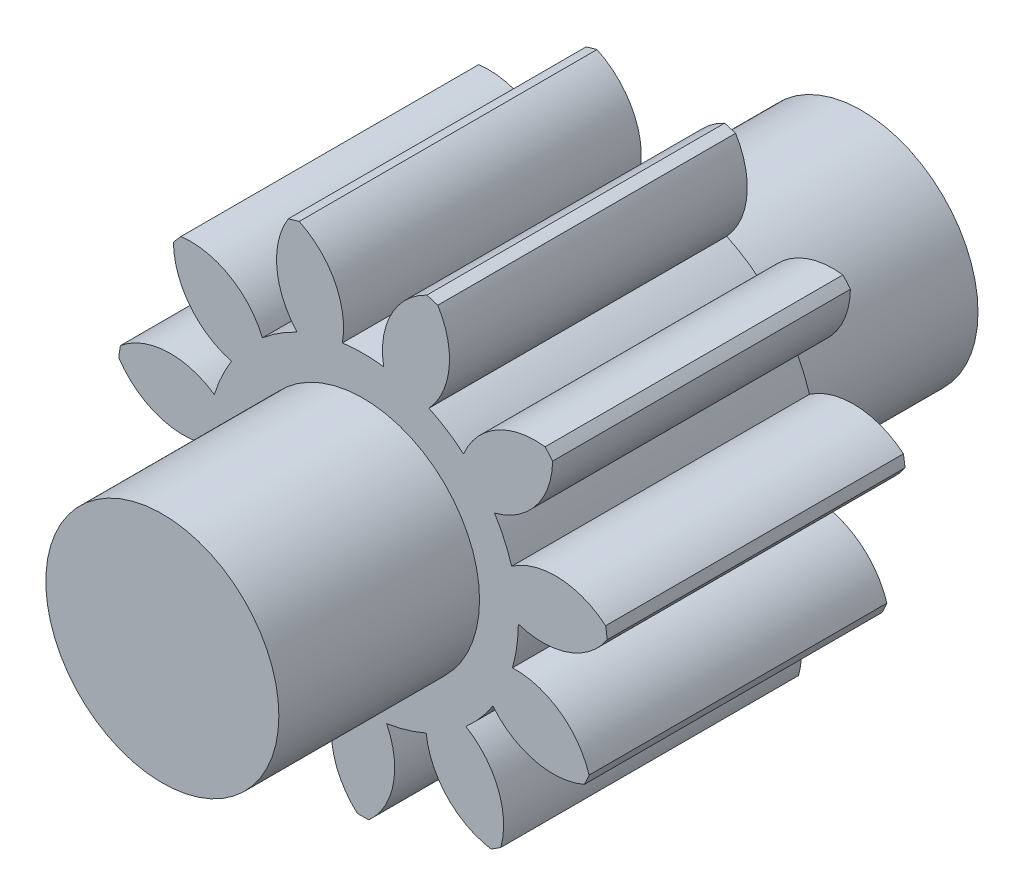
SolidWorks part; units mm, degrees
ref_plane "Front Plane" through (0, 0, 0) normal (0, 0, 1) x (1, 0, 0)
ref_plane "Top Plane" through (0, 0, 0) normal (0, 1, 0) x (1, 0, 0)
ref_plane "Right Plane" through (0, 0, 0) normal (1, 0, 0) x (0, 0, -1)
sketch "Sketch1" plane through (0, 0, 0) normal (0, 0, 1) x (1, 0, 0)
  circle A0 centre (0, 0) radius 9
  dimension "D1" = 18
extrude "Boss-Extrude1" add sketch "Sketch1" along normal mid plane 54
sketch "Sketch2" plane through (0, 0, 0) normal (0, 0, 1) x (1, 0, 0)
  line L0 (0, 35.33) -> (0, -35.33) construction
  arc A1 (1.5924, 11.8939) -> (-1.5924, 11.8939) centre (0, 0) ccw
  arc A3 (1.823, -11.8607) -> (0.443, -18.9948) centre (-3.555, -14.5209) cw
  arc A4 (-1.823, -11.8607) -> (-0.443, -18.9948) centre (3.555, -14.5209) ccw
  arc A5 (-14.0652, 12.7738) -> (-14.6454, 12.1042) centre (0, 0) ccw
  arc A8 (-4.8788, -10.9635) -> (-9.8967, -16.219) centre (-10.8413, -10.2938) cw
  arc A9 (-7.946, -8.9923) -> (-10.6421, -15.74) centre (-4.8599, -14.1378) ccw
  arc A10 (-10.0316, -6.5854) -> (-17.0943, -8.2937) centre (-14.6855, -2.7984) cw
  arc A11 (-11.5462, -3.2689) -> (-17.4623, -7.4878) centre (-11.7319, -9.266) ccw
  arc A12 (-11.9994, -0.1165) -> (-18.8645, 2.2648) centre (-13.8672, 5.5854) cw
  arc A13 (-11.4806, 3.4924) -> (-18.7385, 3.1417) centre (-14.8791, -1.4523) ccw
  arc A14 (-10.1575, 6.3894) -> (-14.6454, 12.1042) centre (-8.6461, 12.1959) cw
  arc A15 (-7.7699, 9.1448) -> (-14.0652, 12.7738) centre (-13.3023, 6.8225) ccw
  arc A16 (-5.0907, 10.8667) -> (-5.7765, 18.1006) centre (-0.68, 14.9343) cw
  arc A17 (-1.5924, 11.8939) -> (-4.9264, 18.3502) centre (-7.5021, 12.9312) ccw
  arc A18 (1.5924, 11.8939) -> (4.9264, 18.3502) centre (7.5021, 12.9312) cw
  arc A19 (5.0907, 10.8667) -> (5.7765, 18.1006) centre (0.68, 14.9343) ccw
  arc A20 (7.7699, 9.1448) -> (14.0652, 12.7738) centre (13.3023, 6.8225) cw
  arc A21 (10.1575, 6.3894) -> (14.6454, 12.1042) centre (8.6461, 12.1959) ccw
  arc A22 (11.4806, 3.4924) -> (18.7385, 3.1417) centre (14.8791, -1.4523) cw
  arc A23 (11.9994, -0.1165) -> (18.8645, 2.2648) centre (13.8672, 5.5854) ccw
  arc A24 (11.5462, -3.2689) -> (17.4623, -7.4878) centre (11.7319, -9.266) cw
  arc A25 (10.0316, -6.5854) -> (17.0943, -8.2937) centre (14.6855, -2.7984) ccw
  arc A26 (7.946, -8.9923) -> (10.6421, -15.74) centre (4.8599, -14.1378) cw
  arc A27 (4.8788, -10.9635) -> (9.8967, -16.219) centre (10.8413, -10.2938) ccw
  arc A28 (-18.7385, 3.1417) -> (-18.8645, 2.2648) centre (0, 0) ccw
  arc A29 (-4.9264, 18.3502) -> (-5.7765, 18.1006) centre (0, 0) ccw
  arc A30 (5.7765, 18.1006) -> (4.9264, 18.3502) centre (0, 0) ccw
  arc A31 (14.6454, 12.1042) -> (14.0652, 12.7738) centre (0, 0) ccw
  arc A32 (18.8645, 2.2648) -> (18.7385, 3.1417) centre (0, 0) ccw
  arc A33 (17.0943, -8.2937) -> (17.4623, -7.4878) centre (0, 0) ccw
  arc A34 (9.8967, -16.219) -> (10.6421, -15.74) centre (0, 0) ccw
  arc A35 (-0.443, -18.9948) -> (0.443, -18.9948) centre (0, 0) ccw
  arc A36 (-10.6421, -15.74) -> (-9.8967, -16.219) centre (0, 0) ccw
  arc A37 (-17.4623, -7.4878) -> (-17.0943, -8.2937) centre (0, 0) ccw
  arc A38 (7.7699, 9.1448) -> (5.0907, 10.8667) centre (0, 0) ccw
  arc A39 (11.4806, 3.4924) -> (10.1575, 6.3894) centre (0, 0) ccw
  arc A40 (11.5462, -3.2689) -> (11.9994, -0.1165) centre (0, 0) ccw
  arc A41 (7.946, -8.9923) -> (10.0316, -6.5854) centre (0, 0) ccw
  arc A42 (1.823, -11.8607) -> (4.8788, -10.9635) centre (0, 0) ccw
  arc A43 (-4.8788, -10.9635) -> (-1.823, -11.8607) centre (0, 0) ccw
  arc A44 (-10.0316, -6.5854) -> (-7.946, -8.9923) centre (0, 0) ccw
  arc A45 (-11.9994, -0.1165) -> (-11.5462, -3.2689) centre (0, 0) ccw
  arc A46 (-10.1575, 6.3894) -> (-11.4806, 3.4924) centre (0, 0) ccw
  arc A47 (-5.0907, 10.8667) -> (-7.7699, 9.1448) centre (0, 0) ccw
  point P6 (0, 0)
  point P77 (0, 0)
  dimension "D1" = 24
  dimension "D2" = 6
  dimension "D3" = 38
  dimension "D4" = 11
extrude "Boss-Extrude2" add sketch "Sketch2" along normal mid plane 23
